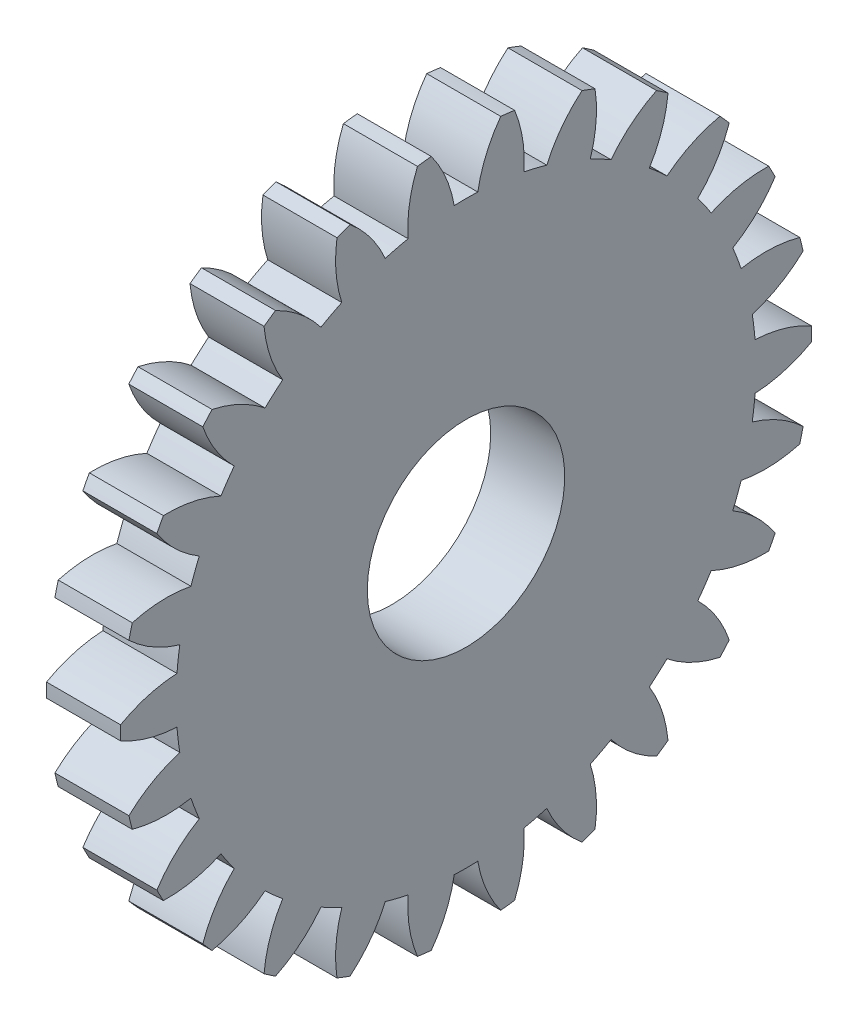
SolidWorks part; units mm, degrees
ref_plane "Plane1" through (0, 0, 0) normal (0, 0, 1) x (1, 0, 0)
ref_plane "Plane2" through (0, 0, 0) normal (0, 1, 0) x (1, 0, 0)
ref_plane "Plane3" through (0, 0, 0) normal (1, 0, 0) x (0, 0, -1)
sketch "HoldingSke" plane through (0, 0, 0) normal (0, 1, 0) x (1, 0, 0)
  line L0 (0, 0) -> (0.8988, -0.4384)
  line L1 (-15, 0) -> (100, 0) construction
  line L2 (0, 0) -> (-2.1039, 2.3779)
  line L3 (0, 0) -> (-11.863, 4.5341)
  line L4 (0, 0) -> (7.762, 3.7858)
  line L5 (0, 0) -> (-46.8476, -17.4728)
  line L6 (0, 0) -> (-2.4869, -1.6779)
  line L7 (-2.1039, 2.3779) -> (8.6586, 51.2059)
  line L8 (-76.2, 54.61) -> (-74.8, 54.61)
  line L9 (-71.009, 38.7566) -> (-53.1078, 45.2721)
  line L10 (-76.2, 71.12) -> (104.1128, 71.12)
  line L11 (0, 0) -> (-3, 0)
  line L12 (-76.2, 101.6) -> (-76.162, 101.6)
  line L13 (24.9733, 27.94) -> (52.9518, 28.4284)
  line L14 (24.9733, 27.94) -> (24.9743, 27.94)
  line L15 (24.9733, 27.94) -> (100.4006, 29.5858)
  line L16 (-63.627, -1) -> (-12.827, -1)
  circle A0 centre (0, 0) radius 4
  circle A1 centre (0, 0) radius 11.749
  circle A2 centre (0, 0) radius 37.5
  circle A3 centre (0, 0) radius 4
  dimension "MHD" = 23.498
  dimension "Hub_dia" = 75
  dimension "Bore" = 8
  dimension "MBD" = 8
  dimension "Num_teeth" = 26
  dimension "Pitch" = 1
  dimension "Overall_len" = 50
  dimension "Show_teeth" = 26
  dimension "Thickness" = 3
  dimension "OAL" = 50.0001
  dimension "T_dim" = 1.4
  dimension "Ap" = 20
  dimension "H" = 19.05
  dimension "Pitch_radius" = 180.3128
  dimension "Width" = 3
  dimension "Backlash" = 0.038
  dimension "Addendum_fac" = 1
  dimension "Dedendum_fac" = 1.25
  dimension "Clearance_fac" = 0.25
  dimension "Dedendum_add" = 0.001
  dimension "Module" = 1
sketch "BasProSke" plane through (0, 0, 0) normal (0, 1, 0) x (1, 0, 0)
  line L0 (-10, 0) -> (60, 0) construction
  line L1 (0, 0) -> (0, 14)
  line L2 (0, 0) -> (3, 0)
  line L3 (3, 0) -> (3, 14)
  line L4 (3, 14) -> (0, 14)
  dimension "Thickness" = 3
  dimension "Diameter" = 28
revolve "Base-Revolve" add sketch "BasProSke" angle 360 about L0
sketch "TooCutSke" plane through (0, 0, 0) normal (1, 0, 0) x (0, 0, -1)
  line L1 (0, 0) -> (0, 107) construction
  line L2 (0, 0) -> (-0.8514, 12.9721) construction
  line L3 (0, 0) -> (-3.1292, 25.771) construction
  line L4 (-0.8514, 12.9721) -> (-1.5646, 12.8855) construction
  arc A0 (0.477, 11.7393) -> (-0.477, 11.7393) centre (0, 0) ccw
  arc A1 (1.4241, 13.9529) -> (-1.4241, 13.9529) centre (0, 0) ccw
  circle A2 centre (0, 0) radius 13 construction
  circle A3 centre (0, 0) radius 12.216 construction
  arc A4 (-0.477, 11.7393) -> (-1.4241, 13.9529) centre (-5.6014, 10.8561) ccw
  arc A5 (1.4241, 13.9529) -> (0.477, 11.7393) centre (5.6014, 10.8561) ccw
  dimension "Root_dia" = 23.498
  dimension "Overcut_dia" = 28.0508
  dimension "Pitch_dia" = 26
  dimension "Base_dia" = 24.432
  dimension "Flank_rad" = 5.2
  dimension "Half_ang" = 6.923
  dimension "Half_CT" = 0.7184
extrude "ToothCut" cut sketch "TooCutSke" along normal through all
fillet "Breaks" [suppressed] radius 0.02
fillet "RootFillets" [suppressed] radius 0.251
pattern_circular "TeethCuts" count 26 every 13.846 about axis through (-10, 0, 0) along (1, 0, 0) of "ToothCut", "RootFillets", "Breaks"
sketch "HubNeaOneSke" plane through (0, 0, 0) normal (-1, 0, 0) x (0, 0, 1)
  circle A0 centre (0, 0) radius 11.749
  dimension "Diameter" = 23.498
extrude "HubNearOne" [suppressed] add sketch "HubNeaOneSke" along normal blind 47.0001
sketch "HubNeaBotSke" plane through (0, 0, 0) normal (-1, 0, 0) x (0, 0, 1)
  circle A0 centre (0, 0) radius 11.749
  dimension "Diameter" = 23.498
extrude "HubNearBoth" [suppressed] add sketch "HubNeaBotSke" along normal blind 23.5
ref_plane "FarPln" through (3, 0, 0) normal (1, 0, 0) x (0, 0, -1)
sketch "HubFarSke" plane through (3, 0, 0) normal (1, 0, 0) x (0, 0, -1)
  circle A0 centre (0, 0) radius 11.749
  dimension "Diameter" = 23.498
extrude "HubFar" [suppressed] add sketch "HubFarSke" along normal blind 23.5
sketch "BorSke" plane through (0, 0, 0) normal (1, 0, 0) x (0, 0, -1)
  circle A0 centre (0, 0) radius 4
  dimension "Diameter" = 8
extrude "Bore" cut sketch "BorSke" along normal mid plane 100.0001
sketch "KeySke" plane through (0, 0, 0) normal (1, 0, 0) x (0, 0, -1)
  line L0 (-1, 0) -> (-1, 5.4)
  line L1 (-1, 5.4) -> (1, 5.4)
  line L2 (1, 5.4) -> (1, 0)
  line L3 (0, 0) -> (0, 34) construction
  line L4 (-1, 0) -> (1, 0)
  dimension "Offset" = 5.4
  dimension "Width" = 2
extrude "Keyway" [suppressed] cut sketch "KeySke" along normal mid plane 100.0001
pattern_circular "Keyway2" [suppressed] count 2 every 90 about axis through (-10, 0, 0) along (1, 0, 0)
equation "' \"Module@HoldingSke\" = 6.35"
equation "' \"Num_teeth@HoldingSke\" = 12"
equation "' \"Ap@HoldingSke\" =  20"
equation "' \"Ap@HoldingSke\" = 20"
equation "' \"Width@HoldingSke\" = 0.5 * 25.4"
equation "' \"Hub_dia@HoldingSke\"= 1 * 25.4"
equation "' \"Hub_dia@HoldingSke\" = 1 * 25.4"
equation "' \"Overall_len@HoldingSke\" = 1.0 * 25.4"
equation "' \"Bore@HoldingSke\" = 0.75 * 25.4"
equation "' \"T_dim@HoldingSke\" = 0.1 * 25.4"
equation "' \"Width@KeySke\" = 0.25 * 25.4"
equation "' \"Show_teeth@HoldingSke\" = 13"
equation "' \"Backlash@HoldingSke\" = 0.009 * 25.4"
equation "' \"Addendum_fac@HoldingSke\" = 1.0"
equation "' \"Dedendum_fac@HoldingSke\" = 1.25"
equation "' \"Dedendum_add@HoldingSke\" = 0.00005 * 25.4"
equation "' \"Clearance_fac@HoldingSke\" = 0.25"
equation "\"Pitch@HoldingSke\" = 1 / \"Module@HoldingSke\""
equation "\"Overcut_dia@TooCutSke\" = (\"Num_teeth@HoldingSke\" + 2 * \"Addendum_fac@HoldingSke\") / \"Pitch@HoldingSke\" + 0.002 * 25.4"
equation "\"Pitch_dia@TooCutSke\" = \"Num_teeth@HoldingSke\" / \"Pitch@HoldingSke\""
equation "\"Base_dia@TooCutSke\" = \"Num_teeth@HoldingSke\" / \"Pitch@HoldingSke\" * cos((\"Ap@HoldingSke\"  * 3.14159265 / 180))"
equation "\"Root_dia@TooCutSke\" = (\"Num_teeth@HoldingSke\" + 2) / \"Pitch@HoldingSke\" - 2 * (\"Addendum_fac@HoldingSke\" + \"Dedendum_fac@HoldingSke\") / \"Pitch@HoldingSke\" - \"Dedendum_add@HoldingSke\" * 2"
equation "\"Half_ang@TooCutSke\" = 180 / \"Num_teeth@HoldingSke\""
equation "\"Half_CT@TooCutSke\" = \"Num_teeth@HoldingSke\" / \"Pitch@HoldingSke\" * sin((3.14159265 / 2 / \"Num_teeth@HoldingSke\")) / 2 - 7 * \"Backlash@HoldingSke\" / 4"
equation "\"Flank_rad@TooCutSke\" = \"Num_teeth@HoldingSke\" / \"Pitch@HoldingSke\" / 5"
equation "\"Radius@RootFillets\" = \"Clearance_fac@HoldingSke\" / \"Pitch@HoldingSke\" + \"Dedendum_add@HoldingSke\""
equation "\"Break_rad@Breaks\" = 0.02 / \"Pitch@HoldingSke\""
equation "\"Thickness@HoldingSke\" = \"Width@HoldingSke\""
equation "\"OAL@HoldingSke\" = \"Thickness@HoldingSke\""
equation "\"MHD@HoldingSke\" = (\"Num_teeth@HoldingSke\" + 2) / \"Pitch@HoldingSke\" - 2 * (\"Addendum_fac@HoldingSke\" + \"Dedendum_fac@HoldingSke\")  / \"Pitch@HoldingSke\" - \"Dedendum_add@HoldingSke\" * 2"
equation "\"MBD@HoldingSke\" = (\"Num_teeth@HoldingSke\" + 2) / \"Pitch@HoldingSke\" - 2 * (\"Addendum_fac@HoldingSke\" + \"Dedendum_fac@HoldingSke\")  / \"Pitch@HoldingSke\" - \"Dedendum_add@HoldingSke\" * 2 - 0.002 * 25.4"
equation "\"MHD@HoldingSke\" = ((sgn( \"MHD@HoldingSke\" - \"Hub_dia@HoldingSke\" )-1)*( \"MHD@HoldingSke\" - \"Hub_dia@HoldingSke\" ))/-2+ \"Hub_dia@HoldingSke\""
equation "\"MBD@HoldingSke\" = ((sgn( \"MBD@HoldingSke\" - \"Bore@HoldingSke\" )-1)*( \"MBD@HoldingSke\" - \"Bore@HoldingSke\" ))/-2+ \"Bore@HoldingSke\""
equation "\"OAL@HoldingSke\" = ((sgn( \"OAL@HoldingSke\" - \"Overall_len@HoldingSke\" )+1)*( \"OAL@HoldingSke\" - \"Overall_len@HoldingSke\" ))/2 + \"Overall_len@HoldingSke\" + 0.000002 * 25.4"
equation "\"Num_teeth@TeethCuts\" = int( \"Show_teeth@HoldingSke\" ) + 1"
equation "\"Num_teeth@TeethCuts\" = ((sgn( \"Num_teeth@TeethCuts\" - \"Num_teeth@HoldingSke\" )-1)*( \"Num_teeth@TeethCuts\" - \"Num_teeth@HoldingSke\" ))/-2+ \"Num_teeth@HoldingSke\""
equation "\"Num_teeth@TeethCuts\" = ((sgn( \"Num_teeth@TeethCuts\" - 2.0)+1)*( \"Num_teeth@TeethCuts\" - 2.0))/2 +2.0"
equation "\"Angle@TeethCuts\" = 360.0 / \"Num_teeth@HoldingSke\""
equation "\"Diameter@BasProSke\" = (\"Num_teeth@HoldingSke\" + 2 * \"Addendum_fac@HoldingSke\") / \"Pitch@HoldingSke\""
equation "\"Thickness@BasProSke\"  = \"Thickness@HoldingSke\""
equation "' \"Fillet_rad@BasProSke\" =  \"Thickness@HoldingSke\" * 0.05"
equation "' \"Fillet_rad@BasProSke\" = \"Thickness@HoldingSke\" * 0.05"
equation "\"MHD@HoldingSke\" = ((sgn( \"MHD@HoldingSke\" - \"Root_dia@TooCutSke\" )-1)*( \"MHD@HoldingSke\" - \"Root_dia@TooCutSke\" ))/-2+ \"Root_dia@TooCutSke\""
equation "\"Diameter@HubNeaOneSke\" = \"MHD@HoldingSke\""
equation "\"Length@HubNearOne\" = \"OAL@HoldingSke\" - \"Thickness@BasProSke\""
equation "\"Diameter@HubNeaBotSke\" = \"MHD@HoldingSke\""
equation "\"Length@HubNearBoth\" = ( \"OAL@HoldingSke\" - \"Thickness@BasProSke\" ) / 2.0"
equation "\"Thickness@FarPln\" = \"Thickness@BasProSke\""
equation "\"Diameter@HubFarSke\" = \"MHD@HoldingSke\""
equation "\"Length@HubFar\" = ( \"OAL@HoldingSke\" - \"Thickness@BasProSke\" ) / 2.0"
equation "\"Diameter@BorSke\" = \"MBD@HoldingSke\""
equation "\"D1@Bore\" = \"OAL@HoldingSke\" * 2.0"
equation "\"D1@Keyway\" = \"OAL@HoldingSke\" * 2.0"
equation "\"Offset@KeySke\" = \"T_dim@HoldingSke\" + \"MBD@HoldingSke\" / 2.0"
